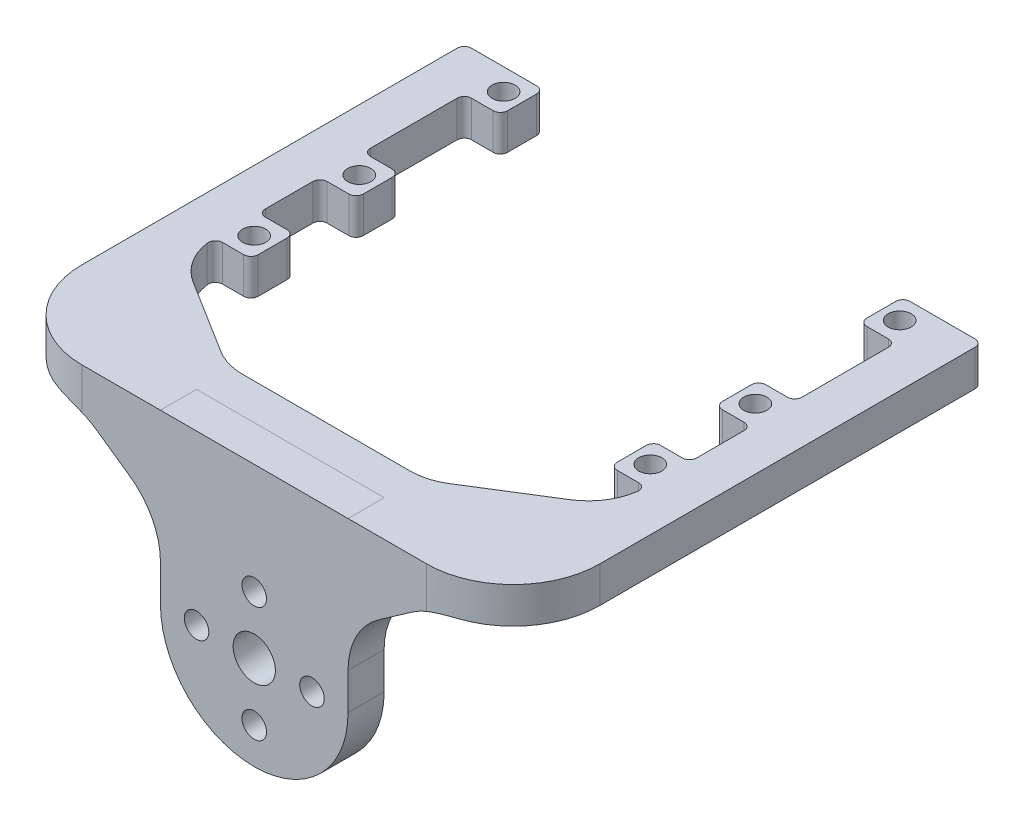
SolidWorks part; units mm, degrees
ref_plane "前视基准面" through (0, 0, 0) normal (0, 0, 1) x (1, 0, 0)
ref_plane "上视基准面" through (0, 0, 0) normal (0, 1, 0) x (1, 0, 0)
ref_plane "右视基准面" through (0, 0, 0) normal (1, 0, 0) x (0, 0, -1)
sketch "草图1" plane through (0, 0, 0) normal (0, 0, 1) x (1, 0, 0)
  line L0 (0, 148.5) -> (0, -94.9538) construction
  line L1 (105, -148.5) -> (-105, -148.5) construction
  line L2 (105, -148.5) -> (105, 148.5) construction
  line L3 (105, 148.5) -> (-105, 148.5) construction
  line L4 (-105, -148.5) -> (-105, 148.5) construction
  line L5 (105, -148.5) -> (-105, 148.5) construction
  line L6 (105, 148.5) -> (-105, -148.5) construction
  line L7 (35.8892, 121.6645) -> (-35.8892, 121.6645)
  line L8 (-35.8892, 121.6645) -> (-66.9017, 102.292)
  line L9 (-75, 40.9339) -> (-75, 31.2613)
  line L10 (-66.9017, 102.292) -> (-66.9017, 52.8701)
  line L11 (75, 40.9339) -> (75, 31.2613)
  line L12 (66.9017, 102.292) -> (66.9017, 52.8701)
  line L13 (35.8892, 121.6645) -> (66.9017, 102.292)
  line L14 (-75, 31.2613) -> (75, 31.2613)
  line L15 (-60, -148.5) -> (-60, -91.8129)
  line L16 (-75, 23.94) -> (75, 23.94)
  line L17 (-75, 23.94) -> (-75, 10.5626)
  line L18 (-38.8455, -105.5906) -> (-66.4608, -113.7617)
  line L19 (-66.4608, -113.7617) -> (-70.1743, -102.7328)
  line L20 (75, 23.94) -> (75, 10.5626)
  line L21 (66.4608, -113.7617) -> (70.1743, -102.7328)
  line L22 (38.8455, -105.5906) -> (66.4608, -113.7617)
  line L23 (-105, 93.0519) -> (105, 93.0519)
  line L24 (-105, 63.0519) -> (105, 63.0519)
  line L25 (-105, -90.0629) -> (-70.5337, -90.0629)
  line L26 (-105, -60.0629) -> (-67.4027, -60.0629)
  line L27 (60, -148.5) -> (60, 148.5)
  line L28 (-60, -58.3129) -> (-45, -58.3129)
  line L29 (-60, -61.8129) -> (-45, -61.8129)
  line L30 (-36, -58.3129) -> (-21, -58.3129)
  line L31 (-36, -61.8129) -> (-21, -61.8129)
  line L32 (-60, -88.3129) -> (-45, -88.3129)
  line L33 (-60, -91.8129) -> (-45, -91.8129)
  line L34 (-36, -88.3129) -> (-21, -88.3129)
  line L35 (-36, -91.8129) -> (-21, -91.8129)
  line L36 (-60, -58.3129) -> (-60, 148.5)
  line L37 (-19.25, -90.0629) -> (105, -90.0629)
  line L38 (-19.25, -60.0629) -> (19.25, -60.0629)
  line L39 (-60, -88.3129) -> (-60, -61.8129)
  line L40 (21, -58.3129) -> (36, -58.3129)
  line L41 (45, -58.3129) -> (60, -58.3129)
  line L42 (60, -61.8129) -> (45, -61.8129)
  line L43 (36, -61.8129) -> (21, -61.8129)
  line L44 (21, -88.3129) -> (36, -88.3129)
  line L45 (21, -91.8129) -> (36, -91.8129)
  line L46 (45, -88.3129) -> (60, -88.3129)
  line L47 (45, -91.8129) -> (60, -91.8129)
  line L48 (37.75, -60.0629) -> (43.25, -60.0629)
  line L49 (58.25, -60.0629) -> (105, -60.0629)
  line L50 (-60, 94.8019) -> (-45, 94.8019)
  line L51 (-36, 94.8019) -> (-21, 94.8019)
  line L52 (-60, 91.3019) -> (-45, 91.3019)
  line L53 (-36, 91.3019) -> (-21, 91.3019)
  line L54 (-60, 64.8019) -> (-45, 64.8019)
  line L55 (-60, 61.3019) -> (-45, 61.3019)
  line L56 (-36, 64.8019) -> (-21, 64.8019)
  line L57 (-36, 61.3019) -> (-21, 61.3019)
  line L58 (21, 94.8019) -> (36, 94.8019)
  line L59 (21, 91.3019) -> (36, 91.3019)
  line L60 (45, 94.8019) -> (60, 94.8019)
  line L61 (45, 91.3019) -> (60, 91.3019)
  line L62 (21, 61.3019) -> (36, 61.3019)
  line L63 (21, 64.8019) -> (36, 64.8019)
  line L64 (45, 61.3019) -> (60, 61.3019)
  line L65 (45, 64.8019) -> (60, 64.8019)
  line L66 (-33.1709, -104.7687) -> (33.1709, -104.7687)
  line L67 (0, -104.7687) -> (0, -148.5) construction
  arc A0 (-75, 40.9339) -> (-66.9017, 52.8701) centre (-79.7474, 52.8701) ccw
  arc A1 (75, 40.9339) -> (66.9017, 52.8701) centre (79.7474, 52.8701) cw
  arc A3 (-60, -88.3129) -> (-60, -91.8129) centre (-60, -90.0629) ccw
  arc A4 (-60, -58.3129) -> (-60, -61.8129) centre (-60, -60.0629) ccw
  circle A5 centre (-60, 63.0519) radius 1.75
  circle A6 centre (-60, 93.0519) radius 1.75
  circle A7 centre (60, 93.0519) radius 1.75
  circle A8 centre (60, 63.0519) radius 1.75
  arc A9 (60, -91.8129) -> (60, -88.3129) centre (60, -90.0629) ccw
  arc A10 (60, -61.8129) -> (60, -58.3129) centre (60, -60.0629) ccw
  arc A11 (-36, -58.3129) -> (-36, -61.8129) centre (-36, -60.0629) ccw
  arc A12 (-36, -88.3129) -> (-36, -91.8129) centre (-36, -90.0629) ccw
  arc A13 (36, -61.8129) -> (36, -58.3129) centre (36, -60.0629) ccw
  arc A14 (36, -91.8129) -> (36, -88.3129) centre (36, -90.0629) ccw
  arc A15 (-45, -61.8129) -> (-45, -58.3129) centre (-45, -60.0629) ccw
  arc A16 (-21, -61.8129) -> (-21, -58.3129) centre (-21, -60.0629) ccw
  arc A17 (-45, -91.8129) -> (-45, -88.3129) centre (-45, -90.0629) ccw
  arc A18 (-21, -91.8129) -> (-21, -88.3129) centre (-21, -90.0629) ccw
  arc A19 (45, -58.3129) -> (45, -61.8129) centre (45, -60.0629) ccw
  arc A20 (21, -58.3129) -> (21, -61.8129) centre (21, -60.0629) ccw
  arc A21 (21, -88.3129) -> (21, -91.8129) centre (21, -90.0629) ccw
  arc A22 (45, -88.3129) -> (45, -91.8129) centre (45, -90.0629) ccw
  circle A23 centre (-36, 93.0519) radius 1.75
  circle A24 centre (-36, 63.0519) radius 1.75
  circle A25 centre (36, 93.0519) radius 1.75
  circle A26 centre (36, 63.0519) radius 1.75
  circle A27 centre (-45, 93.0519) radius 1.75
  circle A28 centre (-21, 93.0519) radius 1.75
  circle A29 centre (-45, 63.0519) radius 1.75
  circle A30 centre (-21, 63.0519) radius 1.75
  circle A31 centre (21, 93.0519) radius 1.75
  circle A32 centre (21, 63.0519) radius 1.75
  circle A33 centre (45, 93.0519) radius 1.75
  circle A34 centre (45, 63.0519) radius 1.75
  arc A35 (33.1709, -104.7687) -> (38.8455, -105.5906) centre (33.1709, -124.7687) cw
  arc A36 (-33.1709, -104.7687) -> (-38.8455, -105.5906) centre (-33.1709, -124.7687) ccw
  spline S0 degree 3 poles (-75, 10.5626) (-72.6959, 1.9073) (-70.3396, -13.3728) (-67.1028, -43.6255) (-66.7657, -72.9327) (-71.8903, -95.1489) (-70.1743, -102.7328) knots 0 0 0 0 0.235247 0.406294 0.801186 1 1 1 1
  spline S1 degree 3 poles (75, 10.5626) (72.6959, 1.9073) (70.3396, -13.3728) (67.1028, -43.6255) (66.7657, -72.9327) (71.8903, -95.1489) (70.1743, -102.7328) knots 0 0 0 0 0.235247 0.406294 0.801186 1 1 1 1
  point P0 (0, 0)
  point P27 (0, 121.6645)
  point P42 (0, -94.0966)
  dimension "D1" = 60
  dimension "D4" = 20
  dimension "D5" = 24
  dimension "D7" = 24
  dimension "D9" = 15
  dimension "D10" = 15
  dimension "D13" = 24
  dimension "D17" = 15
  dimension "D2" = 30
  dimension "D3" = 30
  dimension "D6" = 24
  dimension "D8" = 24
  dimension "D11" = 15
  dimension "D12" = 15
  dimension "D14" = 24
  dimension "D15" = 24
  dimension "D16" = 24
  dimension "D18" = 15
  dimension "D19" = 15
  dimension "D20" = 15
  dimension "D21" = 15
  dimension "D22" = 15
  dimension "D23" = 15
  dimension "D24" = 15
  dimension "D25" = 15
  dimension "D26" = 15
  dimension "D27" = 15
  dimension "D28" = 15
  dimension "D29" = 3.5
  dimension "D30" = 3.5
  dimension "D31" = 3.5
extrude "凸台-拉伸1" add sketch "草图1" along normal blind 3
sketch "草图7" plane through (0, 0, 0) normal (0, 0, -1) x (-1, 0, 0)
  line L0 (0, 121.6645) -> (0, -104.7687) construction
  line L1 (-35.8892, 121.6645) -> (35.8892, 121.6645) construction
  line L2 (33.1709, -104.7687) -> (-33.1709, -104.7687) construction
  line L3 (0, 41.2613) -> (-21, 41.2613) construction
  line L4 (0, 41.2613) -> (21, 41.2613) construction
  line L5 (0, 13.94) -> (-21, 13.94) construction
  line L6 (0, 13.94) -> (21, 13.94) construction
  line L7 (75, 23.94) -> (-75, 23.94) construction
  line L8 (75, 31.2613) -> (-75, 31.2613) construction
  circle A0 centre (-21, 41.2613) radius 2.25
  circle A1 centre (21, 41.2613) radius 2.25
  circle A2 centre (-21, 13.94) radius 2.25
  circle A3 centre (21, 13.94) radius 2.25
  dimension "D1" = 10
  dimension "D2" = 10
extrude "切除-拉伸2" cut sketch "草图7" against normal through all
sketch "草图8" plane through (0, 0, 3) normal (0, 0, 1) x (1, 0, 0)
  line L0 (0, 121.6645) -> (0, -1.9696) construction
  line L1 (35.8892, 121.6645) -> (-35.8892, 121.6645) construction
  line L2 (-33.1709, -104.7687) -> (33.1709, -104.7687) construction
  line L3 (-33.409, 20.409) -> (-12.6214, -0.3786)
  line L4 (31.818, -51.182) -> (-31.818, -51.182)
  line L5 (35, -48) -> (35, 15.6418)
  line L8 (-35, 18.818) -> (-12.6214, -3.5605) construction
  line L9 (-33.409, -52.773) -> (-12.5737, -31.9377)
  line L10 (-36.591, 17.227) -> (-15.8034, -3.5605)
  line L11 (33.4105, 20.4105) -> (12.573, -0.427)
  line L12 (15.803, -3.5609) -> (36.5881, 17.2241)
  line L13 (31.8195, 18.8195) -> (-31.818, 18.818)
  line L14 (-15.8038, -28.8038) -> (-36.591, -49.591)
  line L15 (12.5534, -31.9174) -> (33.409, -52.773)
  line L16 (34.9993, 18.8173) -> (12.6207, -3.5613) construction
  line L17 (0, -30.3951) -> (0, -104.7687) construction
  line L18 (-35, -48) -> (-35, 15.636)
  line L19 (-11.9624, -1.9696) -> (-14.2124, -1.9696) construction
  line L20 (15.8034, -28.8034) -> (36.591, -49.591)
  line L21 (14.2117, -30.3951) -> (11.9607, -30.3951) construction
  line L22 (14.2117, -30.3951) -> (14.2117, -28.1441) construction
  line L23 (14.2117, -1.9696) -> (11.9612, -1.9696) construction
  line L24 (-14.2124, -30.3951) -> (-14.2124, -28.1446) construction
  line L25 (14.2117, -30.3951) -> (12.62, -28.8034) construction
  line L26 (14.2117, -1.9696) -> (12.6204, -3.5609) construction
  line L27 (12.6207, -28.8027) -> (35, -51.182) construction
  line L28 (-12.6215, -3.5606) -> (-14.2124, -1.9696) construction
  line L29 (-14.2124, -4.2196) -> (-14.2124, -1.9696) construction
  line L30 (-12.6214, -28.8034) -> (-35, -51.182) construction
  line L31 (-12.6211, -28.8037) -> (-14.2124, -30.3951) construction
  line L32 (-11.9619, -30.3951) -> (-14.2124, -30.3951) construction
  line L33 (14.2117, -4.2201) -> (14.2117, -1.9696) construction
  line L34 (11.0312, -30.3951) -> (0, -30.3951) construction
  arc A0 (-33.409, 20.409) -> (-36.591, 17.227) centre (-35, 18.818) ccw
  arc A1 (36.5881, 17.2241) -> (33.4105, 20.4105) centre (34.9993, 18.8173) ccw
  arc A2 (-36.591, -49.591) -> (-33.409, -52.773) centre (-35, -51.182) ccw
  arc A3 (33.409, -52.773) -> (36.591, -49.591) centre (35, -51.182) ccw
  arc A4 (-15.8034, -3.5605) -> (-12.6214, -0.3786) centre (-14.2124, -1.9696) ccw
  arc A5 (12.6692, -0.3308) -> (15.803, -3.5609) centre (14.2117, -1.9696) ccw
  arc A6 (-12.6699, -32.0338) -> (-15.8038, -28.8038) centre (-14.2124, -30.3951) ccw
  arc A7 (15.8034, -28.8034) -> (12.6894, -32.0534) centre (14.2117, -30.3951) ccw
  circle A8 centre (-0.0004, -16.1823) radius 8
  point P6 (0, -16.182)
  point P13 (-0.0004, -16.1823)
extrude "切除-拉伸3" cut sketch "草图8" against normal through all
sketch "草图9" plane through (0, 0, 3) normal (0, 0, 1) x (1, 0, 0)
  line L0 (-70.7828, -98.747) -> (70.7828, -98.747) construction
  line L1 (0, -98.747) -> (0, -104.7687) construction
  line L2 (55, -100.497) -> (20, -100.497)
  line L3 (-55, -96.997) -> (-20, -96.997)
  line L4 (-55, -100.497) -> (-20, -100.497)
  line L5 (-33.1709, -104.7687) -> (33.1709, -104.7687) construction
  line L6 (55, -96.997) -> (20, -96.997)
  arc A0 (-55, -96.997) -> (-55, -100.497) centre (-55, -98.747) ccw
  arc A1 (-20, -100.497) -> (-20, -96.997) centre (-20, -98.747) ccw
  arc A2 (20, -100.497) -> (20, -96.997) centre (20, -98.747) cw
  arc A3 (55, -96.997) -> (55, -100.497) centre (55, -98.747) cw
  spline S0 degree 3 poles (-75, 10.5626) (-72.6959, 1.9073) (-70.3396, -13.3728) (-67.1028, -43.6255) (-66.7657, -72.9327) (-71.8903, -95.1489) (-70.1743, -102.7328) knots 0 0 0 0 0.235247 0.406294 0.801186 1 1 1 1 construction
  spline S1 degree 3 poles (75, 10.5626) (72.6959, 1.9073) (70.3396, -13.3728) (67.1028, -43.6255) (66.7657, -72.9327) (71.8903, -95.1489) (70.1743, -102.7328) knots 0 0 0 0 0.235247 0.406294 0.801186 1 1 1 1 construction
  dimension "D1" = 35
  dimension "D2" = 20
extrude "切除-拉伸4" cut sketch "草图9" against normal blind 3
sketch "草图10" plane through (0, 0, 3) normal (0, 0, 1) x (1, 0, 0)
  line L0 (-21, -60.0629) -> (-21, -90.0629) construction
  line L1 (21, -60.0629) -> (21, -90.0629) construction
  line L2 (-21, -75.0629) -> (-17.5, -75.0629) construction
  line L4 (12.5, -80.0629) -> (-12.5, -80.0629)
  line L6 (12.5, -70.0629) -> (-12.5, -70.0629)
  line L11 (17.5, -75.0629) -> (21, -75.0629) construction
  arc A0 (-12.5, -70.0629) -> (-12.5, -80.0629) centre (-12.5, -75.0629) ccw
  arc A1 (12.5, -80.0629) -> (12.5, -70.0629) centre (12.5, -75.0629) ccw
  point P11 (0, -75.0629)
extrude "切除-拉伸5" cut sketch "草图10" against normal blind 3
sketch "草图11" plane through (0, 0, 3) normal (0, 0, 1) x (1, 0, 0)
  line L0 (-21, 93.0519) -> (-21, 63.0519) construction
  line L1 (21, 93.0519) -> (21, 63.0519) construction
  line L2 (-21, 78.0519) -> (-20, 78.0519) construction
  line L4 (15, 73.0519) -> (-15, 73.0519)
  line L6 (15, 83.0519) -> (-15, 83.0519)
  line L10 (20, 78.0519) -> (21, 78.0519) construction
  arc A0 (-15, 83.0519) -> (-15, 73.0519) centre (-15, 78.0519) ccw
  arc A1 (15, 73.0519) -> (15, 83.0519) centre (15, 78.0519) ccw
  point P10 (0, 78.0519)
  dimension "D1" = 30
extrude "切除-拉伸8" cut sketch "草图11" against normal blind 3
sketch "草图12" plane through (0, 0, 3) normal (0, 0, 1) x (1, 0, 0)
  line L0 (0, 121.6645) -> (0, 83.0519) construction
  line L1 (35.8892, 121.6645) -> (-35.8892, 121.6645) construction
  line L2 (15, 83.0519) -> (-15, 83.0519) construction
  circle A0 centre (0, 106.3718) radius 11 construction
  circle A1 centre (0, 106.3718) radius 8 construction
  circle A2 centre (0, 114.3718) radius 1.7
  circle A3 centre (0, 98.3718) radius 1.7
  circle A4 centre (8, 106.3718) radius 1.7
  circle A5 centre (-8, 106.3718) radius 1.7
extrude "切除-拉伸9" cut sketch "草图12" against normal blind 3
sketch "草图13" plane through (0, 0, 3) normal (0, 0, 1) x (1, 0, 0)
  line L0 (0, -104.7687) -> (0, -80.0629) construction
  line L1 (-33.1709, -104.7687) -> (33.1709, -104.7687) construction
  line L2 (-12.5, -80.0629) -> (12.5, -80.0629) construction
  circle A0 centre (0, -92.4158) radius 8 construction
  circle A1 centre (0, -84.4158) radius 1.7
  circle A2 centre (8, -92.4158) radius 1.7
  circle A3 centre (0, -100.4158) radius 1.7
  circle A4 centre (-8, -92.4158) radius 1.7
extrude "切除-拉伸11" cut sketch "草图13" against normal blind 3
sketch "草图14" plane through (0, 0, 3) normal (0, 0, 1) x (1, 0, 0)
  line L0 (0, 23.94) -> (0, -104.7687) construction
  line L1 (-55.4755, 8.9197) -> (-55.4755, -46.0803)
  line L2 (-58.9755, 8.9197) -> (-58.9755, -46.0803)
  line L3 (-75, 23.94) -> (75, 23.94) construction
  line L4 (-33.1709, -104.7687) -> (33.1709, -104.7687) construction
  line L5 (58.9755, 8.9197) -> (58.9755, -46.0803)
  line L6 (55.4755, 8.9197) -> (55.4755, -46.0803)
  arc A0 (-55.4755, 8.9197) -> (-58.9755, 8.9197) centre (-57.2255, 8.9197) ccw
  arc A1 (-58.9755, -46.0803) -> (-55.4755, -46.0803) centre (-57.2255, -46.0803) ccw
  arc A2 (58.9755, -46.0803) -> (55.4755, -46.0803) centre (57.2255, -46.0803) cw
  arc A3 (55.4755, 8.9197) -> (58.9755, 8.9197) centre (57.2255, 8.9197) cw
extrude "切除-拉伸12" cut sketch "草图14" against normal through all
fillet "圆角1" radius 2 2 edges at (75, 31.2613, 1.5) (-75, 31.2613, 1.5)
fillet "圆角2" radius 2 2 edges at (-75, 23.94, 1.5) (75, 23.94, 1.5)
sketch "草图15" plane through (0, 0, 0) normal (0, 0, -1) x (-1, 0, 0)
  line L0 (0, 121.6645) -> (0, 31.2613) construction
  line L1 (-35.8892, 121.6645) -> (35.8892, 121.6645) construction
  line L2 (73, 31.2613) -> (-73, 31.2613) construction
  line L3 (-27.5188, 121.6645) -> (-63.6963, 99.0657) construction
  line L4 (-35.8892, 121.6645) -> (-66.9017, 102.292) construction
  line L5 (-61.1842, 102.4035) -> (-34.7748, 118.9006)
  line L6 (-59.5948, 99.8591) -> (-33.1854, 116.3562)
  line L7 (27.5188, 121.6645) -> (63.6963, 99.0657) construction
  line L8 (59.5948, 99.8591) -> (33.1854, 116.3562)
  line L9 (61.1842, 102.4035) -> (34.7748, 118.9006)
  arc A0 (-61.1842, 102.4035) -> (-59.5948, 99.8591) centre (-60.3895, 101.1313) ccw
  arc A1 (-33.1854, 116.3562) -> (-34.7748, 118.9006) centre (-33.9801, 117.6284) ccw
  arc A2 (33.1854, 116.3562) -> (34.7748, 118.9006) centre (33.9801, 117.6284) cw
  arc A3 (61.1842, 102.4035) -> (59.5948, 99.8591) centre (60.3895, 101.1313) cw
extrude "切除-拉伸13" cut sketch "草图15" against normal through all
sketch "草图16" plane through (0, 0, 0) normal (0, 0, -1) x (-1, 0, 0)
  line L0 (0, 121.6645) -> (0, 31.2613) construction
  line L1 (-35.8892, 121.6645) -> (35.8892, 121.6645) construction
  line L2 (73, 31.2613) -> (-73, 31.2613) construction
  line L3 (-21, 41.2613) -> (-66.71, 41.2613) construction
  line L4 (-61.517, 42.7613) -> (-32.0563, 42.7613)
  line L5 (-61.517, 39.7613) -> (-32.0563, 39.7613)
  line L6 (21, 41.2613) -> (66.71, 41.2613) construction
  line L7 (61.517, 39.7613) -> (32.0563, 39.7613)
  line L8 (61.517, 42.7613) -> (32.0563, 42.7613)
  arc A0 (-61.517, 42.7613) -> (-61.517, 39.7613) centre (-61.517, 41.2613) ccw
  arc A1 (-32.0563, 39.7613) -> (-32.0563, 42.7613) centre (-32.0563, 41.2613) ccw
  arc A2 (32.0563, 39.7613) -> (32.0563, 42.7613) centre (32.0563, 41.2613) cw
  arc A3 (61.517, 42.7613) -> (61.517, 39.7613) centre (61.517, 41.2613) cw
extrude "切除-拉伸14" cut sketch "草图16" against normal through all
sketch "草图17" plane through (0, 0, 0) normal (0, 0, -1) x (-1, 0, 0)
  text T0 "Y" font "黑体" height in points 72
extrude "切除-拉伸15" cut sketch "草图17" against normal through all
sketch "草图18" plane through (0, 0, 0) normal (0, 0, -1) x (-1, 0, 0)
  text T0 "H" font "黑体" height in points 72
extrude "切除-拉伸16" cut sketch "草图18" against normal through all
sketch "草图19" plane through (0, 0, 0) normal (0, 0, -1) x (-1, 0, 0)
  line L1 (-87.3022, 27.5246) -> (87.3022, 27.5246)
  line L2 (-87.3022, 27.5246) -> (-87.3022, -126.2702)
  line L3 (-87.3022, -126.2702) -> (87.3022, -126.2702)
  line L4 (87.3022, 27.5246) -> (87.3022, -126.2702)
extrude "切除-拉伸17" cut sketch "草图19" against normal blind 10
ref_plane "基准面1" through (0, 0, 13) normal (0, 0, 1) x (1, 0, 0)
sketch "草图20" plane through (0, 0, 13) normal (0, 0, 1) x (1, 0, 0)
  line L0 (-13, 106.3718) -> (-13, 129.6645) construction
  line L1 (13, 106.3718) -> (13, 129.6645) construction
  line L2 (35.8892, 121.6645) -> (-35.8892, 121.6645) construction
  line L4 (-13, 106.3718) -> (-13, 129.6645)
  line L5 (-13, 129.6645) -> (13, 129.6645)
  line L6 (13, 106.3718) -> (13, 129.6645)
  circle A0 centre (0, 98.3718) radius 1.7 construction
  circle A1 centre (-8, 106.3718) radius 1.7 construction
  circle A2 centre (8, 106.3718) radius 1.7 construction
  circle A3 centre (0, 114.3718) radius 1.7 construction
  circle A4 centre (0, 98.3718) radius 1.7
  circle A5 centre (-8, 106.3718) radius 1.7
  circle A6 centre (8, 106.3718) radius 1.7
  circle A7 centre (0, 114.3718) radius 1.7
  arc A8 (-13, 106.3718) -> (13, 106.3718) centre (0, 106.3718) ccw
  circle A9 centre (0, 106.3718) radius 2.9291
  dimension "D1" = 8
extrude "凸台-拉伸2" add sketch "草图20" along normal blind 5 separate body
sketch "草图21" plane through (0, 0, 18) normal (0, 0, 1) x (1, 0, 0)
  line L0 (0, 129.6645) -> (0, 124.6645) construction
  line L1 (13, 129.6645) -> (-13, 129.6645) construction
  line L3 (35.8892, 124.6647) -> (-35.8892, 124.6647)
  line L4 (35.8892, 124.6647) -> (35.8892, 129.6644)
  line L5 (35.8892, 129.6644) -> (-35.8892, 129.6644)
  line L6 (-35.8892, 124.6647) -> (-35.8892, 129.6644)
  line L7 (35.8892, 124.6647) -> (-35.8892, 129.6644) construction
  line L8 (35.8892, 129.6644) -> (-35.8892, 124.6647) construction
  point P5 (0, 127.1645)
extrude "凸台-拉伸3" add sketch "草图21" against normal blind 5
sketch "草图22" plane through (0, 0, 18) normal (0, 0, 1) x (1, 0, 0)
  line L0 (-24.4446, 124.6647) -> (-13, 116.6647)
  line L1 (-35.8892, 124.6647) -> (-13, 124.6647) construction
  line L2 (0, 93.3718) -> (0, 129.6645) construction
  line L3 (13, 129.6645) -> (-13, 129.6645) construction
  line L4 (24.4446, 124.6647) -> (13, 116.6647)
  line L5 (-24.4446, 124.6647) -> (-13, 124.6647)
  line L6 (-13, 124.6647) -> (-13, 116.6647)
  line L7 (24.4446, 124.6647) -> (13, 124.6647)
  line L8 (13, 124.6647) -> (13, 116.6647)
  arc A0 (-13, 106.3718) -> (13, 106.3718) centre (0, 106.3718) ccw construction
  dimension "D1" = 8
extrude "凸台-拉伸4" add sketch "草图22" against normal up to surface (5 mm away) up to face at (0, 123.0324, 13)
fillet "圆角3" radius 10 4 edges at (13, 116.6647, 15.5) (24.4446, 124.6647, 15.5) (-13, 116.6647, 15.5) (-24.4446, 124.6647, 15.5)
sketch "草图23" plane through (0, 0, 13) normal (0, 0, -1) x (-1, 0, 0)
  line L1 (-35.8892, 129.6644) -> (35.8892, 129.6644)
  line L2 (-35.8892, 129.6644) -> (-35.8892, 124.6647)
  line L3 (-35.8892, 124.6647) -> (35.8892, 124.6647)
  line L4 (35.8892, 129.6644) -> (35.8892, 124.6647)
extrude "凸台-拉伸5" add sketch "草图23" along normal blind 5
fillet "圆角4" radius 1 1 edges at (0, 124.6647, 13)
sketch "草图24" plane through (0, 0, 8) normal (0, 0, -1) x (-1, 0, 0)
  line L0 (-35.8892, 127.1645) -> (35.8892, 127.1645) construction
  line L1 (-35.8892, 129.6644) -> (-35.8892, 124.6647) construction
  line L2 (35.8892, 124.6647) -> (35.8892, 129.6644) construction
  line L3 (-35.8892, 124.6647) -> (35.8892, 124.6647) construction
  line L4 (-35.8892, 129.6644) -> (-29.8892, 129.6644)
  line L5 (-35.8892, 129.6644) -> (-35.8892, 124.6647)
  line L6 (-35.8892, 124.6647) -> (-29.8892, 124.6647)
  line L7 (-29.8892, 129.6644) -> (-29.8892, 124.6647)
  line L9 (35.8892, 129.6644) -> (29.8892, 129.6644)
  line L10 (35.8892, 129.6644) -> (35.8892, 124.6647)
  line L11 (35.8892, 124.6647) -> (29.8892, 124.6647)
  line L12 (29.8892, 129.6644) -> (29.8892, 124.6647)
extrude "凸台-拉伸7" add sketch "草图24" along normal blind 55
sketch "草图25" plane through (0, 129.6644, 0) normal (0, 1, 0) x (1, 0, 0)
  line L0 (-29.8892, 2) -> (-13.8892, -8)
  line L1 (-29.8892, 47) -> (-29.8892, -8) construction
  line L2 (-29.8892, -8) -> (29.8892, -8) construction
  line L3 (0, -8) -> (0, 42) construction
  line L4 (-29.8892, 2) -> (-29.8892, -8)
  line L5 (-29.8892, -8) -> (-13.8892, -8)
  line L6 (29.8892, -8) -> (13.8892, -8)
  line L7 (29.8892, 2) -> (29.8892, -8)
  line L8 (29.8892, 2) -> (13.8892, -8)
  dimension "D1" = 10
  dimension "D2" = 16
extrude "凸台-拉伸8" add sketch "草图25" against normal up to surface (4.9997 mm away) up to face at (0, 124.6647, -6.3333)
fillet "圆角5" radius 8 4 edges at (13.8892, 127.1645, 8) (29.8892, 127.1645, -2) (-13.8892, 127.1645, 8) (-29.8892, 127.1645, -2)
fillet "圆角6" radius 12 2 edges at (35.8892, 127.1645, 18) (-35.8892, 127.1645, 18)
sketch "草图26" plane through (0, 129.6644, 0) normal (0, 1, 0) x (1, 0, 0)
  line L0 (0, -18) -> (0, 27) construction
  line L1 (13, -18) -> (-13, -18) construction
sketch "草图27" plane through (0, 129.6644, 0) normal (0, 1, 0) x (1, 0, 0)
  line L0 (0, 27) -> (-29.8892, 27) construction
  line L1 (-29.8892, 6.434) -> (-24.8892, 6.434)
  line L2 (-29.8892, 6.434) -> (-29.8892, 12.434)
  line L3 (-29.8892, 12.434) -> (-24.8892, 12.434)
  line L4 (-24.8892, 6.434) -> (-24.8892, 12.434)
  line L9 (-29.8892, 47) -> (-29.8892, 6.434) construction
  line L10 (0, 27) -> (0, -18) construction
  line L11 (-29.8892, 27) -> (-24.8892, 27)
  line L12 (-29.8892, 27) -> (-29.8892, 21)
  line L13 (-29.8892, 21) -> (-24.8892, 21)
  line L14 (-24.8892, 27) -> (-24.8892, 21)
  line L15 (24.8892, 27) -> (24.8892, 21)
  line L16 (29.8892, 21) -> (24.8892, 21)
  line L17 (29.8892, 27) -> (29.8892, 21)
  line L18 (29.8892, 27) -> (24.8892, 27)
  line L23 (24.8892, 6.434) -> (24.8892, 12.434)
  line L24 (29.8892, 12.434) -> (24.8892, 12.434)
  line L25 (29.8892, 6.434) -> (29.8892, 12.434)
  line L26 (29.8892, 6.434) -> (24.8892, 6.434)
  line L27 (-35.8892, 47) -> (-29.8892, 47) construction
  line L28 (-29.8892, 47) -> (-24.8892, 47)
  line L29 (-29.8892, 47) -> (-29.8892, 41)
  line L30 (-29.8892, 41) -> (-24.8892, 41)
  line L31 (-24.8892, 47) -> (-24.8892, 41)
  line L33 (29.8892, 47) -> (24.8892, 47)
  line L34 (29.8892, 47) -> (29.8892, 41)
  line L35 (29.8892, 41) -> (24.8892, 41)
  line L36 (24.8892, 47) -> (24.8892, 41)
extrude "凸台-拉伸9" add sketch "草图27" against normal up to surface (4.9997 mm away) up to face at (0, 124.6647, -5.306)
fillet "圆角7" radius 1 10 edges at (29.8892, 127.1645, -6.434) (29.8892, 127.1645, -12.434) (29.8892, 127.1645, -21) (29.8892, 127.1645, -27) (29.8892, 127.1645, -41) (-29.8892, 127.1645, -41) (-29.8892, 127.1645, -27) (-29.8892, 127.1645, -21) (-29.8892, 127.1645, -12.434) (-29.8892, 127.1645, -6.434)
fillet "圆角8" radius 1 10 edges at (24.8892, 127.1645, -41) (-24.8892, 127.1645, -41) (24.8892, 127.1645, -27) (24.8892, 127.1645, -21) (24.8892, 127.1645, -12.434) (24.8892, 127.1645, -6.434) (-24.8892, 127.1645, -6.434) (-24.8892, 127.1645, -12.434) (-24.8892, 127.1645, -21) (-24.8892, 127.1645, -27)
fillet "圆角9" radius 1 4 edges at (35.8892, 127.1645, -47) (24.8892, 127.1645, -47) (-35.8892, 127.1645, -47) (-24.8892, 127.1645, -47)
sketch "草图28" plane through (0, 129.6644, 0) normal (0, 1, 0) x (1, 0, 0)
  line L0 (-24.8892, 44) -> (-35.8892, 44) construction
  line L1 (-24.8892, 42) -> (-24.8892, 46) construction
  line L2 (-35.8892, 46) -> (-35.8892, -6) construction
  line L3 (-27.4458, 44) -> (-27.4458, 47.064) construction
  line L4 (-27.4458, 44) -> (-27.4458, 3.3304) construction
  line L5 (-24.8892, 24) -> (-35.8892, 24) construction
  line L6 (-24.8892, 22) -> (-24.8892, 26) construction
  line L7 (-24.8892, 9.434) -> (-35.8892, 9.434) construction
  line L8 (-24.8892, 7.434) -> (-24.8892, 11.434) construction
  line L9 (0, -8) -> (0, 47.064) construction
  line L10 (-11.5948, -8) -> (11.5948, -8) construction
  line L11 (27.4458, 44) -> (27.4458, 3.3304) construction
  line L12 (27.4458, 44) -> (27.4458, 47.064) construction
  circle A0 centre (-27.4458, 44) radius 1.6
  circle A1 centre (-27.4458, 24) radius 1.6
  circle A2 centre (-27.4458, 9.434) radius 1.6
  circle A3 centre (27.4458, 9.434) radius 1.6
  circle A4 centre (27.4458, 24) radius 1.6
  circle A5 centre (27.4458, 44) radius 1.6
extrude "切除-拉伸19" cut sketch "草图28" against normal blind 50
sketch "草图29" plane through (0, 0, 0) normal (0, 0, -1) x (-1, 0, 0)
  line L1 (-86.8175, 27.2362) -> (87.5527, 27.2362)
  line L2 (-86.8175, 27.2362) -> (-86.8175, 122.5914)
  line L3 (-86.8175, 122.5914) -> (87.5527, 122.5914)
  line L4 (87.5527, 27.2362) -> (87.5527, 122.5914)
ref_plane "基准面2" through (0, 0, -6.434) normal (0, 0, 1) x (1, 0, 0)
sketch "草图32" plane through (0, 0, -6.434) normal (0, 0, 1) x (1, 0, 0)
  line L0 (35.8892, 134.6644) -> (35.8892, 141.3433) construction
  line L1 (-35.8892, 129.6644) -> (-56.4167, 116.8415)
  line L2 (-35.8892, 129.6644) -> (35.8892, 129.6644)
  line L4 (-35.8892, 134.6644) -> (35.8892, 134.6644)
  line L6 (-35.8892, 134.6644) -> (-58.6633, 120.4381)
  line L7 (-35.8892, 121.6645) -> (-66.9017, 102.292) construction
  line L8 (-56.4167, 116.8415) -> (-58.6633, 120.4381)
  line L9 (0, 129.6644) -> (0, 98.3718) construction
  line L10 (56.4167, 116.8415) -> (58.6633, 120.4381)
  line L11 (35.8892, 134.6644) -> (58.6633, 120.4381)
  line L12 (35.8892, 129.6644) -> (56.4167, 116.8415)
extrude "凸台-拉伸10" add sketch "草图32" against normal up to surface (6 mm away) up to face at (-27.3892, 127.1645, -12.434)
sketch "草图33" plane through (0, 124.6647, 0) normal (0, -1, 0) x (1, 0, 0)
  circle A0 centre (-27.4458, -9.434) radius 1.6 construction
  circle A1 centre (27.4458, -9.434) radius 1.6 construction
  circle A2 centre (-27.4458, -9.434) radius 1.6
  circle A3 centre (27.4458, -9.434) radius 1.6
extrude "切除-拉伸21" cut sketch "草图33" against normal through all
sketch "草图34" plane through (0, 0, 0) normal (0, 0, -1) x (-1, 0, 0)
  line L1 (-80.2126, 29.3415) -> (82.6305, 29.3415)
  line L2 (-80.2126, 29.3415) -> (-80.2126, 122.4549)
  line L3 (-80.2126, 122.4549) -> (82.6305, 122.4549)
  line L4 (82.6305, 29.3415) -> (82.6305, 122.4549)
extrude "切除-拉伸22" cut sketch "草图34" against normal blind 10
sketch "草图35" plane through (0, 134.6644, 0) normal (0, 1, 0) x (1, 0, 0)
  line L0 (0, -8) -> (0, 12.434) construction
  line L1 (-11.5948, -8) -> (11.5948, -8) construction
  line L2 (35.8892, 12.434) -> (-35.8892, 12.434) construction
  line L4 (-24.4458, 6.434) -> (-30.4458, 6.434)
  line L5 (-24.4458, 6.434) -> (-24.4458, 12.434)
  line L6 (-24.4458, 12.434) -> (-30.4458, 12.434)
  line L7 (-30.4458, 6.434) -> (-30.4458, 12.434)
  line L8 (-24.4458, 6.434) -> (-30.4458, 12.434) construction
  line L9 (-24.4458, 12.434) -> (-30.4458, 6.434) construction
  line L10 (30.4458, 6.434) -> (24.4458, 6.434)
  line L11 (30.4458, 6.434) -> (30.4458, 12.434)
  line L12 (30.4458, 12.434) -> (24.4458, 12.434)
  line L13 (24.4458, 6.434) -> (24.4458, 12.434)
  line L14 (30.4458, 6.434) -> (24.4458, 12.434) construction
  line L15 (30.4458, 12.434) -> (24.4458, 6.434) construction
  circle A0 centre (-27.4458, 9.434) radius 1.6
  circle A1 centre (27.4458, 9.434) radius 1.6
  point P6 (-27.4458, 9.434)
  point P12 (27.4458, 9.434)
extrude "凸台-拉伸11" add sketch "草图35" along normal blind 1
sketch "草图36" plane through (0, 0, -12.434) normal (0, 0, -1) x (-1, 0, 0)
  line L0 (28.8892, 129.6644) -> (-28.8892, 129.6644)
  line L24 (28.8892, 124.6647) -> (28.8892, 129.6644)
  line L25 (28.8892, 129.6644) -> (35.8892, 129.6644)
  line L26 (35.8892, 129.6644) -> (56.4167, 116.8415)
  line L27 (56.4167, 116.8415) -> (58.6633, 120.4381)
  line L28 (58.6633, 120.4381) -> (35.8892, 134.6644)
  line L29 (35.8892, 134.6644) -> (30.4458, 134.6644)
  line L30 (30.4458, 134.6644) -> (30.4458, 135.6644)
  line L31 (30.4458, 135.6644) -> (24.4458, 135.6644)
  line L32 (24.4458, 135.6644) -> (24.4458, 134.6644)
  line L33 (24.4458, 134.6644) -> (-24.4458, 134.6644)
  line L34 (-24.4458, 134.6644) -> (-24.4458, 135.6644)
  line L35 (-24.4458, 135.6644) -> (-30.4458, 135.6644)
  line L36 (-30.4458, 135.6644) -> (-30.4458, 134.6644)
  line L37 (-30.4458, 134.6644) -> (-35.8892, 134.6644)
  line L38 (-35.8892, 134.6644) -> (-58.6633, 120.4381)
  line L39 (-58.6633, 120.4381) -> (-56.4167, 116.8415)
  line L40 (-56.4167, 116.8415) -> (-35.8892, 129.6644)
  line L41 (-35.8892, 129.6644) -> (-28.8892, 129.6644)
  line L42 (-28.8892, 129.6644) -> (-28.8892, 124.6647)
  line L43 (-28.8892, 124.6647) -> (-25.8892, 124.6647)
  line L44 (-25.8892, 124.6647) -> (-25.8892, 129.6644)
  line L45 (-25.8892, 129.6644) -> (25.8892, 129.6644)
  line L46 (25.8892, 129.6644) -> (25.8892, 124.6647)
  line L47 (25.8892, 124.6647) -> (28.8892, 124.6647)
  line L49 (28.8892, 129.6644) -> (35.8892, 129.6644)
  line L50 (35.8892, 129.6644) -> (56.4167, 116.8415)
  line L51 (56.4167, 116.8415) -> (58.6633, 120.4381)
  line L52 (58.6633, 120.4381) -> (35.8892, 134.6644)
  line L53 (35.8892, 134.6644) -> (30.4458, 134.6644)
  line L54 (30.4458, 134.6644) -> (30.4458, 135.6644)
  line L55 (30.4458, 135.6644) -> (24.4458, 135.6644)
  line L56 (24.4458, 135.6644) -> (24.4458, 134.6644)
  line L57 (24.4458, 134.6644) -> (-24.4458, 134.6644)
  line L58 (-24.4458, 134.6644) -> (-24.4458, 135.6644)
  line L59 (-24.4458, 135.6644) -> (-30.4458, 135.6644)
  line L60 (-30.4458, 135.6644) -> (-30.4458, 134.6644)
  line L61 (-30.4458, 134.6644) -> (-35.8892, 134.6644)
  line L62 (-35.8892, 134.6644) -> (-58.6633, 120.4381)
  line L63 (-58.6633, 120.4381) -> (-56.4167, 116.8415)
  line L64 (-56.4167, 116.8415) -> (-35.8892, 129.6644)
  line L65 (-35.8892, 129.6644) -> (-28.8892, 129.6644)
  line L69 (-25.8892, 129.6644) -> (25.8892, 129.6644)
  line M26 (28.8892, 129.6644) -> (35.8892, 129.6644)
  line M27 (35.8892, 129.6644) -> (56.4167, 116.8415)
  line M28 (56.4167, 116.8415) -> (58.6633, 120.4381)
  line M29 (58.6633, 120.4381) -> (35.8892, 134.6644)
  line M30 (35.8892, 134.6644) -> (30.4458, 134.6644)
  line M31 (30.4458, 134.6644) -> (30.4458, 135.6644)
  line M32 (30.4458, 135.6644) -> (24.4458, 135.6644)
  line M33 (24.4458, 135.6644) -> (24.4458, 134.6644)
  line M34 (24.4458, 134.6644) -> (-24.4458, 134.6644)
  line M35 (-24.4458, 134.6644) -> (-24.4458, 135.6644)
  line M36 (-24.4458, 135.6644) -> (-30.4458, 135.6644)
  line M37 (-30.4458, 135.6644) -> (-30.4458, 134.6644)
  line M38 (-30.4458, 134.6644) -> (-35.8892, 134.6644)
  line M39 (-35.8892, 134.6644) -> (-58.6633, 120.4381)
  line M40 (-58.6633, 120.4381) -> (-56.4167, 116.8415)
  line M41 (-56.4167, 116.8415) -> (-35.8892, 129.6644)
  line M42 (-35.8892, 129.6644) -> (-28.8892, 129.6644)
  line M46 (-25.8892, 129.6644) -> (25.8892, 129.6644)
  dimension "D1" = 0
extrude "切除-拉伸24" cut sketch "草图36" against normal blind 10 contours L0 M26 M27 M28 M29 M30 M31 M32 M33 M34 M35 M36 M37 M38 M39 M40 M41 M42 M46
